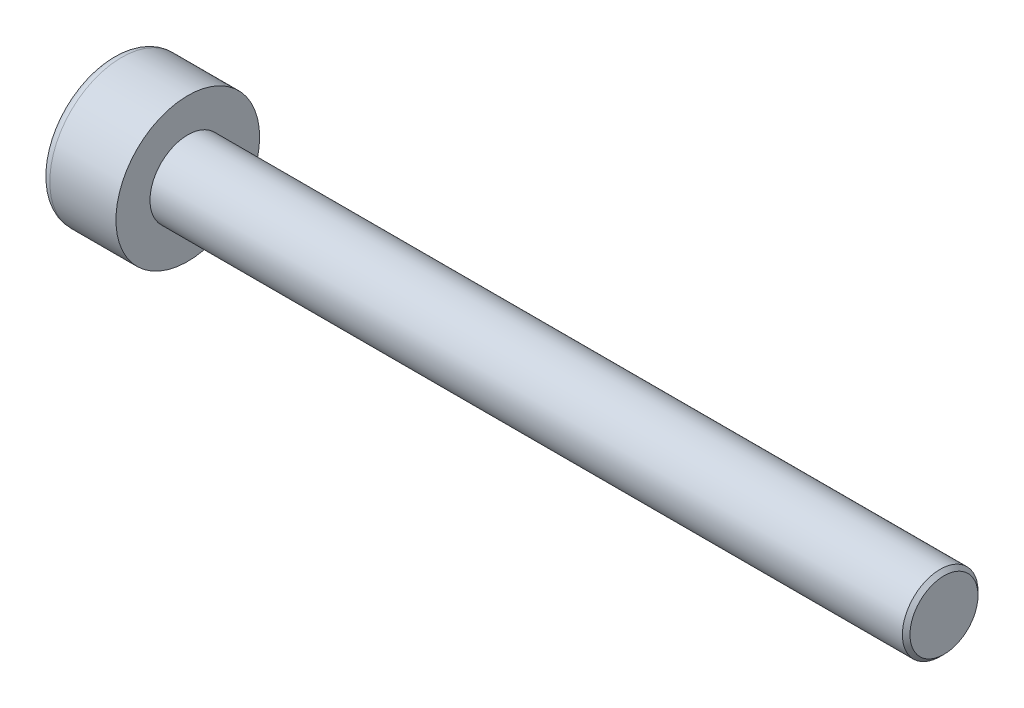
SolidWorks part; units mm, degrees
ref_plane "Front" through (0, 0, 0) normal (0, 0, 1) x (1, 0, 0)
ref_plane "Top" through (0, 0, 0) normal (0, 1, 0) x (1, 0, 0)
ref_plane "Right" through (0, 0, 0) normal (1, 0, 0) x (0, 0, -1)
sketch "Sketch1" plane through (0, 0, 0) normal (1, 0, 0) x (0, 0, -1)
  circle A0 centre (0, 0) radius 1.9
  dimension "dk" = 3.8
extrude "BaseHead" add sketch "Sketch1" along normal blind 2
sketch "Sketch2" plane through (2, 0, 0) normal (1, 0, 0) x (0, 0, -1)
  circle A0 centre (0, 0) radius 1
  dimension "d" = 2
extrude "BaseBody" add sketch "Sketch2" along normal blind 20
cosmetic thread "ThreadCosmetic1" parameters "b"=10, "D2"=1.567
sketch "Sketch3" plane through (0, 0, 0) normal (1, 0, 0) x (0, 0, -1)
  line L1 (0.866, 0) -> (0.433, 0.75)
  line L2 (0.433, 0.75) -> (-0.433, 0.75)
  line L3 (-0.433, 0.75) -> (-0.866, 0)
  line L4 (-0.866, 0) -> (-0.433, -0.75)
  line L5 (-0.433, -0.75) -> (0.433, -0.75)
  line L6 (0.433, -0.75) -> (0.866, 0)
  circle A0 centre (0, 0) radius 0.75 construction
  dimension "s" = 1.5
  dimension "e" = 1.7321
extrude "HexagonSocket" cut sketch "Sketch3" along normal blind 1
sketch "Sketch4" plane through (-4.1961, 0.75, 0) normal (0, 0, 1) x (-1, 0, 0)
  line L0 (-5.1961, 1.5) -> (-5.6292, 0.75)
  line L2 (-5.6292, 0.75) -> (-5.1961, 0.75)
  line L3 (-5.1961, 0.75) -> (-5.1961, 1.5)
  line L4 (-5.0351, 0.75) -> (0.839, 0.75) construction
  line L5 (-26.1961, 0.75) -> (-6.1961, 0.75) construction
  line L6 (-6.1961, 0.75) -> (-4.1961, 0.75) construction
  dimension "m" = 60
revolve "Cut-Revolve1" cut sketch "Sketch4" angle 360 about L4
fillet "HeadFillet" [suppressed] radius 0.1
fillet "TopFillet" radius 0.25 1 edges at (0, 0, -1.9)
chamfer "Chamfer1" distance 0.1 angle 45 1 edges at (22, 0, -1)
sketch "Sketch5" plane through (0, 0, 0) normal (0, 0, 1) x (1, 0, 0)
  line L0 (21.9, 0.8125) -> (22.0083, 1)
  line L1 (22.0083, 1) -> (22.0083, 1.2165)
  line L2 (22.0083, 1.2165) -> (21.7918, 1.2165)
  line L3 (21.7918, 1.2165) -> (21.7918, 1)
  line L4 (21.7918, 1) -> (21.9, 0.8125)
  line L5 (0, 0) -> (7.8886, 0) construction
  line L6 (21.9, -1) -> (21.9, 1) construction
  dimension "D1" = 2
  dimension "D2" = 0.2165
revolve "Cut-Revolve10" [suppressed] cut sketch "Sketch5" angle 360 about L5
pattern_linear "LPattern10" [suppressed] count 38 spacing 0.2598 along (1, 0, 0)
equation "\"r1@TopFillet\" = \"d@Sketch2\" / 8"
equation "\"D1@Chamfer1\" = \"r@HeadFillet\""
equation "\"D1@Sketch5\" = \"d@Sketch2\""
equation "\"D2@Sketch5\" =  ( \"d@Sketch2\" - \"D2@ThreadCosmetic1\" )  / 2"
equation "\"D3@LPattern10\" = \"D2@Sketch5\" * 1.2"
equation "\"D1@LPattern10\" = \"b@ThreadCosmetic1\" / \"D3@LPattern10\""
